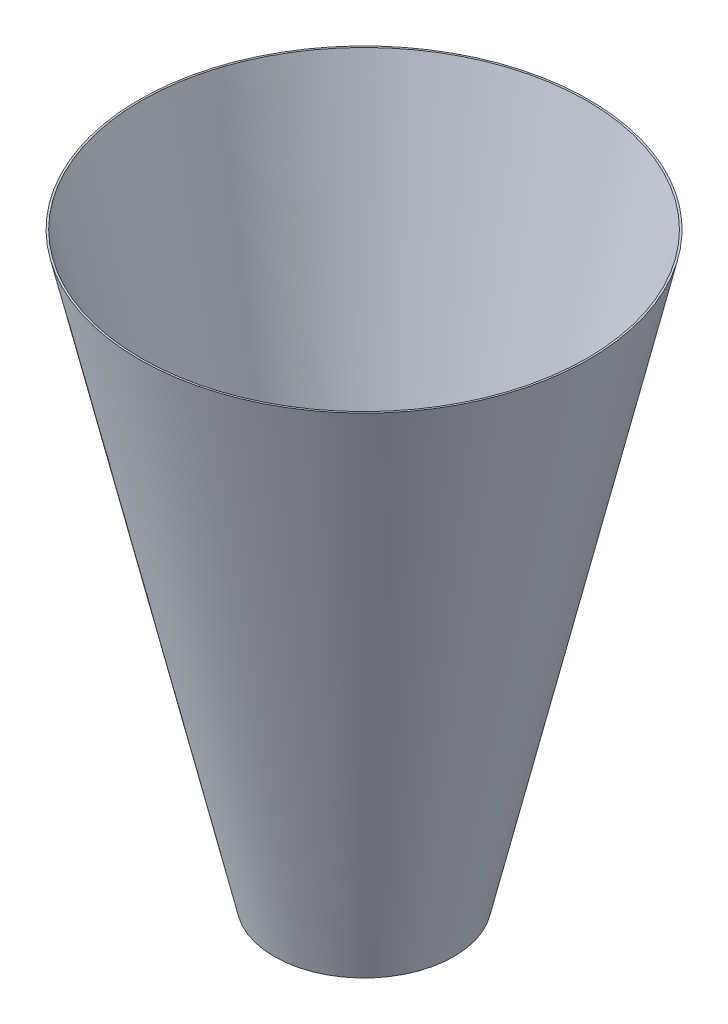
SolidWorks part; units mm, degrees
ref_plane "Front Plane" through (0, 0, 0) normal (0, 0, 1) x (1, 0, 0)
ref_plane "Top Plane" through (0, 0, 0) normal (0, 1, 0) x (1, 0, 0)
ref_plane "Right Plane" through (0, 0, 0) normal (1, 0, 0) x (0, 0, -1)
sketch "Sketch1" plane through (0, 0, 0) normal (0, 0, 1) x (1, 0, 0)
  line L0 (0, 265.3856) -> (0, -175.5196) construction
  line L2 (-100, -650) -> (-250, 0)
  line L3 (-250, 0) -> (-247.9474, 0)
  line L4 (-100, -650) -> (-97.9474, -650)
  line L5 (-247.9474, 0) -> (-97.9474, -650)
  dimension "D1" = 500
  dimension "D2" = 200
  dimension "D3" = 2
  dimension "D4" = 650
revolve "Revolve1" add sketch "Sketch1" angle 360 about L0
